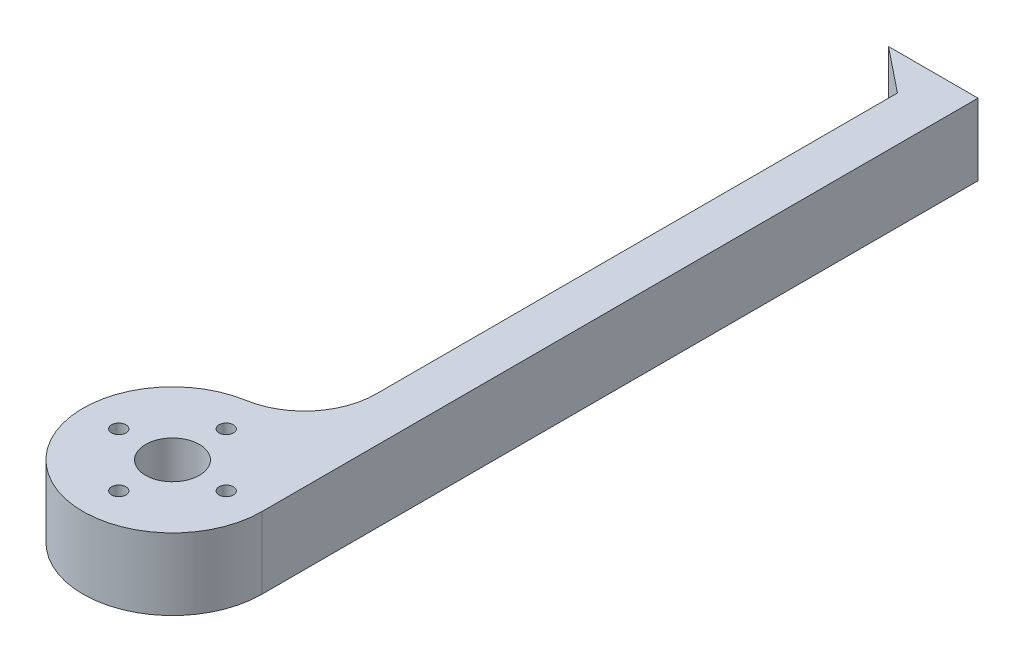
SolidWorks part; units mm, degrees
ref_plane "Alzado" through (0, 0, 0) normal (0, 0, 1) x (1, 0, 0)
ref_plane "Planta" through (0, 0, 0) normal (0, 1, 0) x (1, 0, 0)
ref_plane "Vista lateral" through (0, 0, 0) normal (1, 0, 0) x (0, 0, -1)
sketch "Croquis1" plane through (0, 0, 0) normal (0, 1, 0) x (1, 0, 0)
  line L0 (0, 0) -> (0, 100) construction
  line L1 (6.25, 95) -> (0, 100)
  line L2 (0, 100) -> (12.5, 100)
  line L3 (0, 100) -> (0, 0)
  line L4 (0, 0) -> (12.5, 0)
  line L5 (12.5, 100) -> (12.5, 0)
  line L6 (0, 95) -> (6.25, 95)
  line L7 (0, 95) -> (0, 0)
  line L8 (0, 0) -> (6.25, 0)
  line L9 (6.25, 95) -> (6.25, 0)
  circle A0 centre (0, 0) radius 12.5
  circle A1 centre (0, 0) radius 3.75
  circle A2 centre (0, 7.5) radius 1
  circle A3 centre (7.5, 0) radius 1
  circle A4 centre (0, -7.5) radius 1
  circle A5 centre (-7.5, 0) radius 1
  point P21 (0, 0)
  dimension "D2" = 25
  dimension "D3" = 7.5
  dimension "D6" = 2
  dimension "D1" = 100
  dimension "D4" = 5
  dimension "D5" = 7.5
  dimension "D7" = 4
extrude "Saliente-Extruir1" add sketch "Croquis1" along normal blind 10 contours A0 L5 L2 L1 L9 | A3 L4 A0 L9 | A2 L7 A1 L8 L9 A0 | A3 L4 L8 A1 L7 A2 A0 A5 A4
fillet "Redondeo1" radius 10 1 edges at (6.25, 5, -10.8253)
